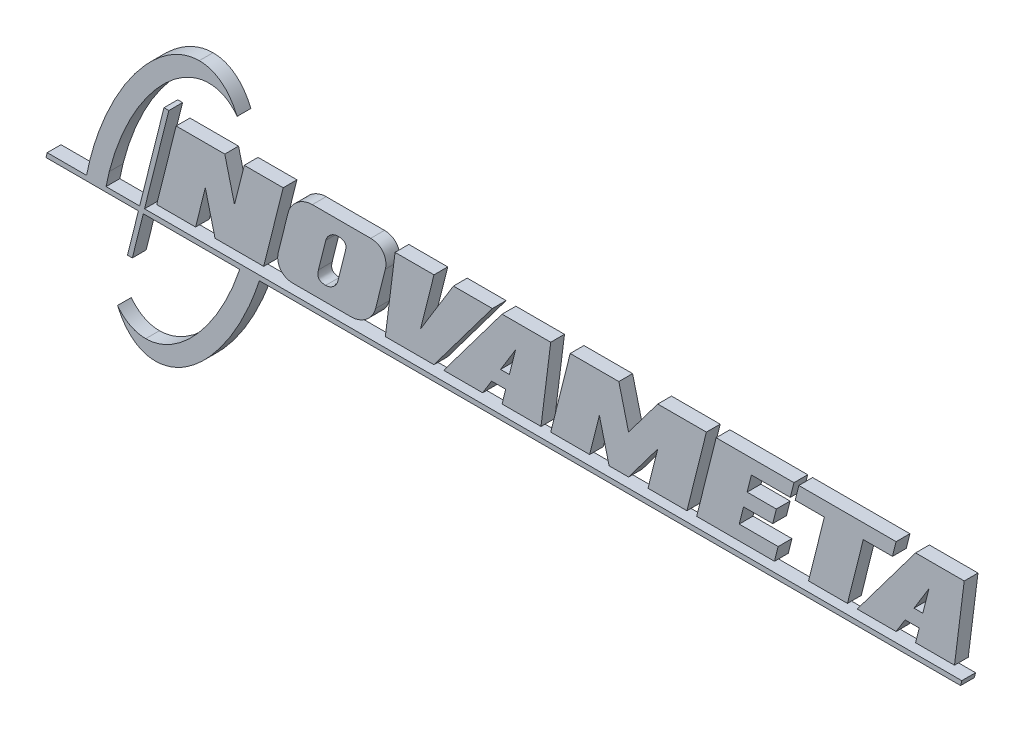
SolidWorks part; units mm, degrees
material "-"
ref_plane "Front Plane" through (0, 0, 0) normal (0, 0, 1) x (1, 0, 0)
ref_plane "Top Plane" through (0, 0, 0) normal (0, 1, 0) x (1, 0, 0)
ref_plane "Right Plane" through (0, 0, 0) normal (1, 0, 0) x (0, 0, -1)
sketch "Model" plane through (0, 0, 0) normal (0, 0, 1) x (1, 0, 0)
  line L0 (190.469, 147.2792) -> (192.4237, 150.4568)
  line L1 (192.4237, 150.4568) -> (195.5023, 150.4582)
  line L2 (195.5023, 150.4582) -> (194.7075, 147.2792)
  line L3 (194.7075, 147.2792) -> (203.1835, 147.2785)
  line L4 (203.1835, 147.2785) -> (205.3043, 164.2325)
  line L5 (205.3043, 164.2325) -> (194.7085, 164.2325)
  line L6 (194.7085, 164.2325) -> (181.9906, 147.2785)
  line L7 (181.9906, 147.2785) -> (190.469, 147.2792)
  line L8 (196.2953, 153.6356) -> (194.3723, 153.6356)
  line L9 (194.3723, 153.6356) -> (197.622, 158.9345)
  line L10 (197.622, 158.9345) -> (196.2953, 153.6356)
  line L11 (171.3959, 147.2799) -> (179.8729, 147.2792)
  line L12 (179.8729, 147.2792) -> (183.3166, 161.0532)
  line L13 (183.3166, 161.0532) -> (189.6752, 161.0539)
  line L14 (189.6752, 161.0539) -> (190.4697, 164.2325)
  line L15 (190.4697, 164.2325) -> (169.2775, 164.2325)
  line L16 (169.2775, 164.2325) -> (168.4827, 161.0539)
  line L17 (168.4827, 161.0539) -> (174.8407, 161.0539)
  line L18 (174.8407, 161.0539) -> (171.3959, 147.2799)
  line L19 (147.025, 147.2792) -> (151.2648, 164.2325)
  line L20 (151.2648, 164.2325) -> (168.2182, 164.2325)
  line L21 (168.2182, 164.2325) -> (167.4234, 161.0539)
  line L22 (167.4234, 161.0539) -> (158.9457, 161.0532)
  line L23 (158.9457, 161.0532) -> (158.0183, 157.3444)
  line L24 (158.0183, 157.3444) -> (164.3769, 157.3444)
  line L25 (164.3769, 157.3444) -> (163.5869, 154.1837)
  line L26 (163.5869, 154.1837) -> (157.2283, 154.1837)
  line L27 (157.2283, 154.1837) -> (156.2964, 150.4568)
  line L28 (156.2964, 150.4568) -> (164.7741, 150.4582)
  line L29 (164.7741, 150.4582) -> (163.9783, 147.2785)
  line L30 (163.9783, 147.2785) -> (147.025, 147.2792)
  line L31 (149.1454, 164.2325) -> (138.5497, 164.2325)
  line L32 (138.5497, 164.2325) -> (132.1914, 155.7557)
  line L33 (132.1914, 155.7557) -> (130.073, 164.2325)
  line L34 (130.073, 164.2325) -> (119.4763, 164.2325)
  line L35 (119.4763, 164.2325) -> (115.2378, 147.2792)
  line L36 (115.2378, 147.2792) -> (123.7137, 147.2792)
  line L37 (123.7137, 147.2792) -> (125.8345, 155.7554)
  line L38 (125.8345, 155.7554) -> (127.9526, 147.2785)
  line L39 (127.9526, 147.2785) -> (132.1904, 147.2785)
  line L40 (132.1904, 147.2785) -> (138.5497, 155.7554)
  line L41 (138.5497, 155.7554) -> (136.4289, 147.2792)
  line L42 (136.4289, 147.2792) -> (144.9055, 147.2792)
  line L43 (144.9055, 147.2792) -> (149.1454, 164.2325)
  line L44 (100.4028, 147.2792) -> (102.3586, 150.4568)
  line L45 (102.3586, 150.4568) -> (105.4365, 150.4582)
  line L46 (105.4365, 150.4582) -> (104.6413, 147.2792)
  line L47 (104.6413, 147.2792) -> (113.1176, 147.2785)
  line L48 (113.1176, 147.2785) -> (115.2388, 164.2325)
  line L49 (115.2388, 164.2325) -> (104.6427, 164.2325)
  line L50 (104.6427, 164.2325) -> (91.9262, 147.2785)
  line L51 (91.9262, 147.2785) -> (100.4028, 147.2792)
  line L52 (106.2306, 153.6356) -> (104.3072, 153.6356)
  line L53 (104.3072, 153.6356) -> (107.5566, 158.9345)
  line L54 (107.5566, 158.9345) -> (106.2306, 153.6356)
  line L55 (89.8074, 147.2792) -> (79.211, 147.2792)
  line L56 (79.211, 147.2792) -> (81.3315, 164.2325)
  line L57 (81.3315, 164.2325) -> (89.8078, 164.2325)
  line L58 (89.8078, 164.2325) -> (86.8936, 152.5766)
  line L59 (86.8936, 152.5766) -> (94.0466, 164.2325)
  line L60 (94.0466, 164.2325) -> (102.5236, 164.2325)
  line L61 (102.5236, 164.2325) -> (89.8074, 147.2792)
  line L62 (29.4094, 147.2785) -> (37.8864, 147.2785)
  line L63 (37.8864, 147.2785) -> (40.0065, 155.7554)
  line L64 (40.0065, 155.7554) -> (42.1246, 147.2785)
  line L65 (42.1246, 147.2785) -> (52.7206, 147.2785)
  line L66 (52.7206, 147.2785) -> (56.9605, 164.2325)
  line L67 (56.9605, 164.2325) -> (48.4842, 164.2325)
  line L68 (48.4842, 164.2325) -> (46.3638, 155.7554)
  line L69 (46.3638, 155.7554) -> (44.2454, 164.2325)
  line L70 (44.2454, 164.2325) -> (33.6489, 164.2325)
  line L71 (33.6489, 164.2325) -> (29.4094, 147.2785)
  line L72 (76.0333, 164.2325) -> (63.3181, 164.2325)
  line L73 (58.0192, 159.9939) -> (55.8998, 151.5168)
  line L74 (59.0786, 147.2792) -> (71.7937, 147.2792)
  line L75 (77.0923, 151.5168) -> (79.2117, 159.9939)
  line L76 (64.6424, 152.5776) -> (66.232, 158.9345)
  line L77 (70.4701, 158.9352) -> (68.8802, 152.5773)
  line L78 (204.5095, 144.1008) -> (204.7741, 145.1605)
  line L79 (204.7741, 145.1605) -> (26.7608, 145.1605)
  line L80 (26.7608, 145.1605) -> (32.0604, 166.3519)
  line L81 (32.0604, 166.3519) -> (31.0003, 166.3519)
  line L82 (31.0003, 166.3519) -> (25.7014, 145.1605)
  line L83 (25.7014, 145.1605) -> (18.3848, 145.1605)
  line L84 (14.1342, 145.1612) -> (5.5697, 145.1612)
  line L85 (5.5697, 145.1612) -> (5.3044, 144.1008)
  line L86 (5.3044, 144.1008) -> (25.4362, 144.1008)
  line L87 (25.4362, 144.1008) -> (23.0515, 134.5641)
  line L88 (23.0515, 134.5641) -> (24.1108, 134.5641)
  line L89 (24.1108, 134.5641) -> (26.4959, 144.1008)
  line L90 (26.4959, 144.1008) -> (47.5117, 144.1008)
  line L91 (51.7719, 144.1008) -> (204.5095, 144.1008)
  spline S0 degree 3 poles (63.3181, 164.2325) (60.9768, 164.2325) (58.6056, 162.3348) (58.0192, 159.9939) knots 1 1 1 1 2 2 2 2
  spline S1 degree 3 poles (55.8998, 151.5168) (55.3145, 149.1766) (56.7376, 147.2792) (59.0786, 147.2792) knots 3 3 3 3 4 4 4 4
  spline S2 degree 3 poles (71.7937, 147.2792) (74.1343, 147.2792) (76.5059, 149.1766) (77.0923, 151.5168) knots 5 5 5 5 6 6 6 6
  spline S3 degree 3 poles (79.2117, 159.9939) (79.7974, 162.3348) (78.3742, 164.2325) (76.0333, 164.2325) knots 7 7 7 7 8 8 8 8
  spline S4 degree 3 poles (66.2316, 150.4575) (64.5101, 150.4575) (64.3485, 151.4059) (64.6424, 152.5776) knots 0 0 0 0 1 1 1 1
  spline S5 degree 3 poles (66.232, 158.9345) (66.5248, 160.105) (67.7103, 161.0536) (68.8809, 161.0536) knots 2 2 2 2 3 3 3 3
  spline S6 degree 3 poles (68.8809, 161.0536) (70.8677, 161.0536) (70.7633, 160.106) (70.4701, 158.9352) knots 3 3 3 3 4 4 4 4
  spline S7 degree 3 poles (68.8802, 152.5773) (68.5881, 151.4066) (67.4016, 150.4575) (66.2316, 150.4575) knots 5 5 5 5 6 6 6 6
  spline S8 degree 3 poles (18.3848, 145.1605) (18.5808, 146.203) (18.8116, 147.2634) (19.0803, 148.3381) knots 6 6 6 6 7 7 7 7
  spline S9 degree 3 poles (19.0803, 148.3381) (22.8858, 163.5537) (32.6123, 175.8875) (40.8041, 175.8875) knots 7 7 7 7 8 8 8 8
  spline S10 degree 3 poles (40.8041, 175.8875) (43.3131, 175.8875) (45.386, 174.7301) (46.9473, 172.6885) knots 8 8 8 8 9 9 9 9
  spline S11 degree 3 poles (46.9473, 172.6885) (45.2193, 176.6869) (42.3971, 179.0668) (38.6864, 179.0668) knots 9 9 9 9 10 10 10 10
  spline S12 degree 3 poles (38.6864, 179.0668) (29.7622, 179.0668) (19.0865, 165.3088) (14.8428, 148.3384) knots 10 10 10 10 11 11 11 11
  spline S13 degree 3 poles (14.8428, 148.3384) (14.5745, 147.2654) (14.3385, 146.205) (14.1342, 145.1612) knots 11 11 11 11 12 12 12 12
  spline S14 degree 3 poles (47.5117, 144.1008) (43.1116, 130.9019) (34.4413, 120.7981) (27.0254, 120.7981) knots 19 19 19 19 20 20 20 20
  spline S15 degree 3 poles (27.0254, 120.7981) (24.5184, 120.7981) (22.4465, 121.9557) (20.8859, 123.9945) knots 20 20 20 20 21 21 21 21
  spline S16 degree 3 poles (20.8859, 123.9945) (22.6136, 119.9982) (25.4355, 117.6197) (29.1445, 117.6197) knots 21 21 21 21 22 22 22 22
  spline S17 degree 3 poles (29.1445, 117.6197) (37.3114, 117.6197) (46.9432, 129.1401) (51.7719, 144.1008) knots 22 22 22 22 23 23 23 23
extrude "Boss-Extrude1" add sketch "Model" along normal blind 3
